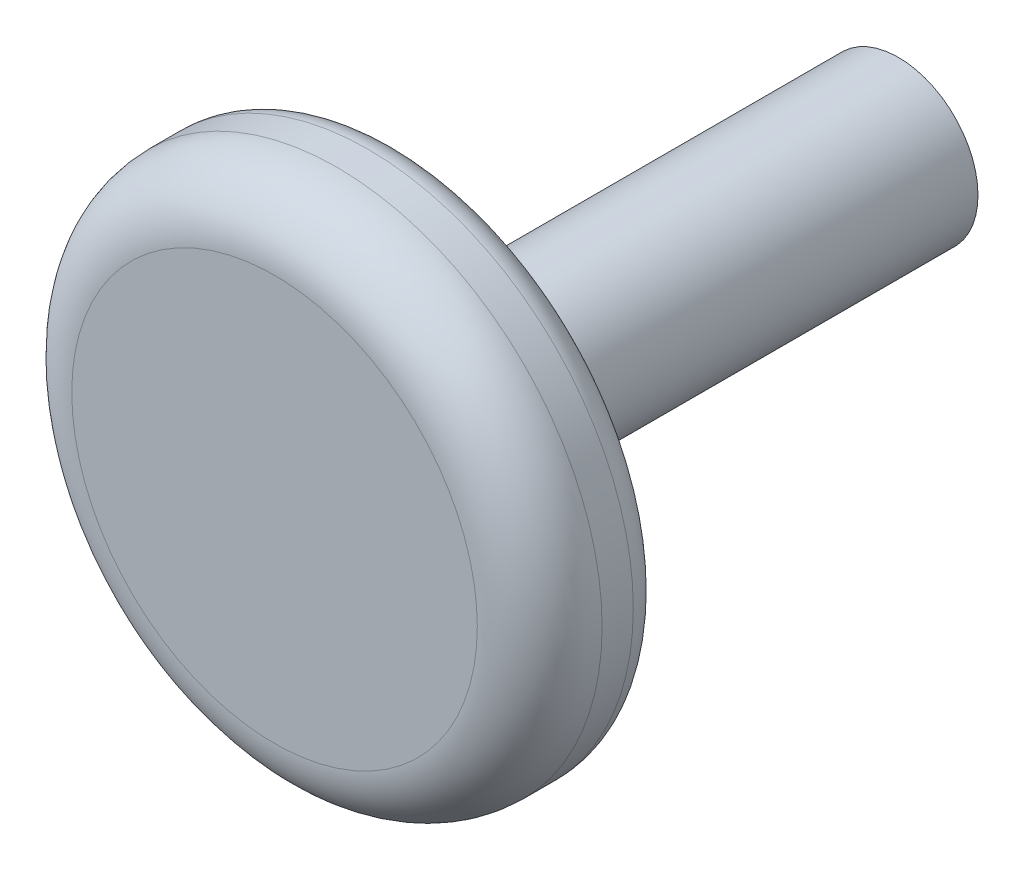
SolidWorks part; units mm, degrees
ref_plane "Alzado" through (0, 0, 0) normal (0, 0, 1) x (1, 0, 0)
ref_plane "Planta" through (0, 0, 0) normal (0, 1, 0) x (1, 0, 0)
ref_plane "Vista lateral" through (0, 0, 0) normal (1, 0, 0) x (0, 0, -1)
sketch "Croquis1" plane through (0, 0, 0) normal (0, 0, 1) x (1, 0, 0)
  line L0 (47, -47) -> (-47, 47) construction
  line L1 (-47, 47) -> (-47, -47) construction
  line L2 (-47, -47) -> (47, 47) construction
  circle A0 centre (0, 0) radius 12.75
  dimension "D1" = 25.5
extrude "Saliente-Extruir1" add sketch "Croquis1" along normal blind 80
sketch "Croquis2" plane through (0, 0, 80) normal (0, 0, 1) x (1, 0, 0)
  circle A0 centre (0, 0) radius 42.5
  dimension "D1" = 85
extrude "Saliente-Extruir2" add sketch "Croquis2" along normal blind 20
fillet "Redondeo1" radius 10 1 edges at (42.5, 0, 100)
sketch "Croquis3" plane through (0, 0, 0) normal (0, 0, -1) x (-1, 0, 0)
  circle A0 centre (0, 0) radius 10.25
  dimension "D1" = 20.5
extrude "Cortar-Extruir1" cut sketch "Croquis3" against normal blind 10
fillet "Redondeo2" radius 10 1 edges at (12.75, 0, 80)
fillet "Redondeo3" radius 5 1 edges at (42.5, 0, 80)
